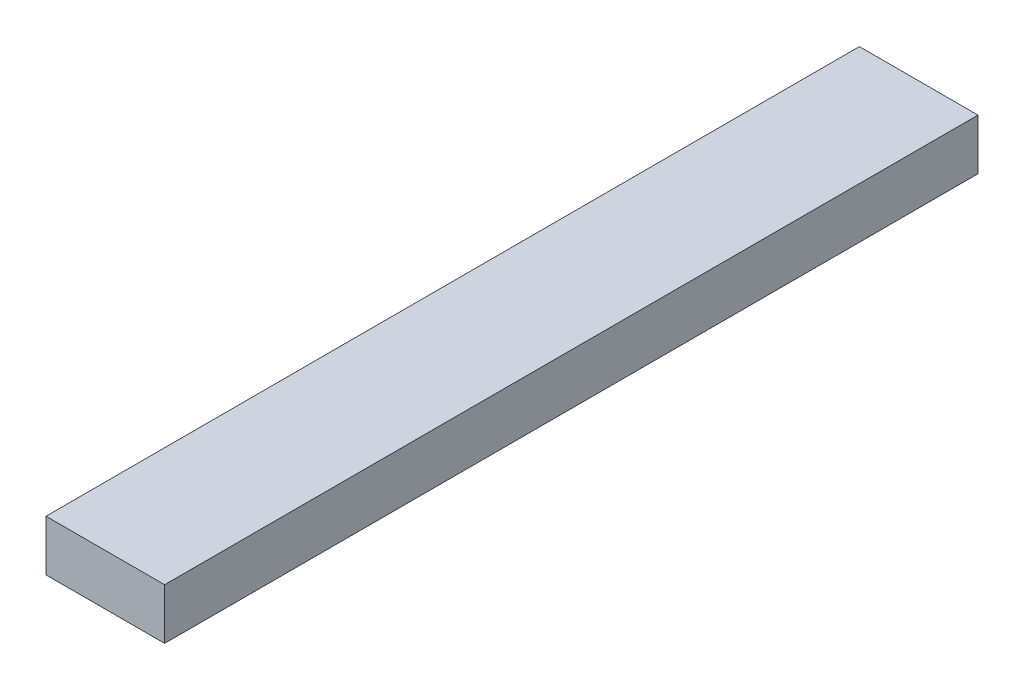
SolidWorks part; units mm, degrees
material "Pine"
ref_plane "Front Plane" through (0, 0, 0) normal (0, 0, 1) x (1, 0, 0)
ref_plane "Top Plane" through (0, 0, 0) normal (0, 1, 0) x (1, 0, 0)
ref_plane "Right Plane" through (0, 0, 0) normal (1, 0, 0) x (0, 0, -1)
sketch "Sketch2" plane through (0, 0, 0) normal (0, 0, 1) x (1, 0, 0)
  line L1 (-88.9, 73.5775) -> (0, 73.5775)
  line L2 (-88.9, 73.5775) -> (-88.9, 35.4775)
  line L3 (-88.9, 35.4775) -> (0, 35.4775)
  line L4 (0, 73.5775) -> (0, 35.4775)
  dimension "D1" = 88.9
  dimension "D2" = 38.1
extrude "Boss-Extrude1" add sketch "Sketch2" along normal blind 609.6
